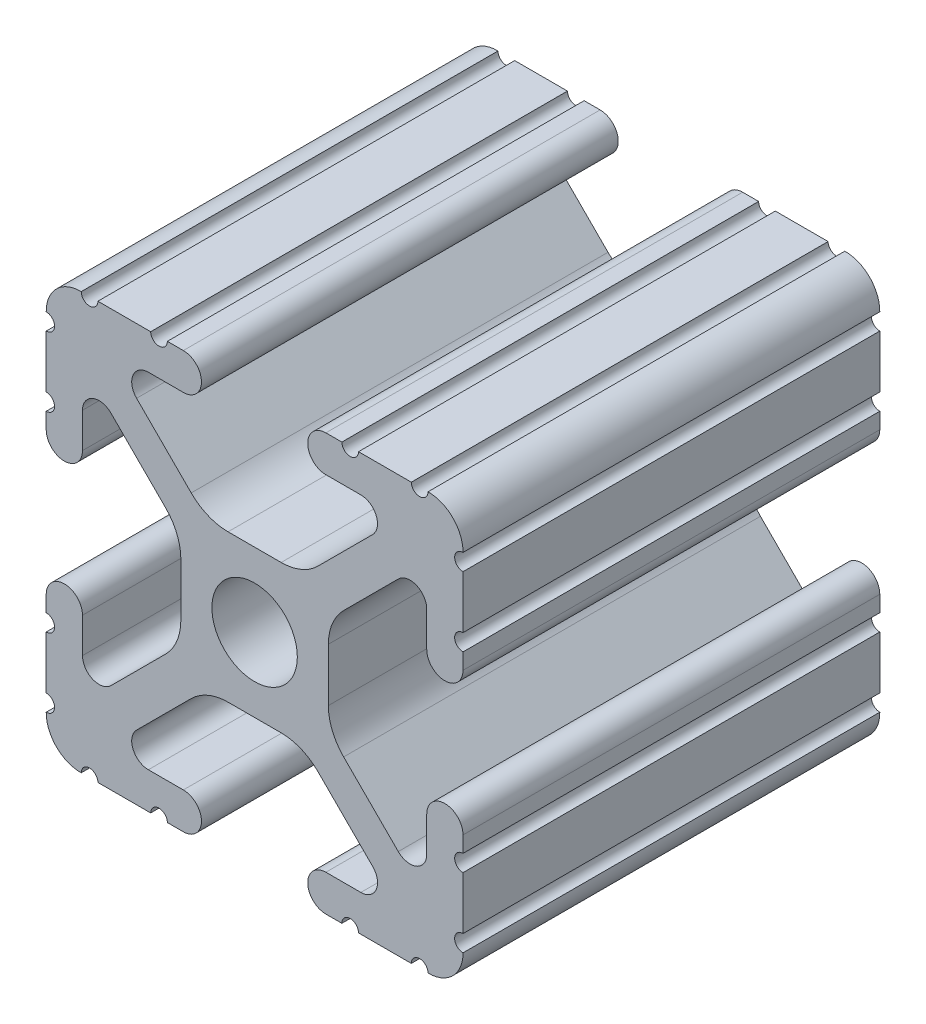
SolidWorks part; units mm, degrees
ref_plane "Front Plane" through (0, 0, 0) normal (0, 0, 1) x (1, 0, 0)
ref_plane "Top Plane" through (0, 0, 0) normal (0, 1, 0) x (1, 0, 0)
ref_plane "Right Plane" through (0, 0, 0) normal (1, 0, 0) x (0, 0, -1)
ref_plane "Plane1" through (0, 0, -25.4) normal (0, 0, -1) x (-1, 0, 0)
sketch "Sketch1" plane through (0, 0, -25.4) normal (0, 0, -1) x (-1, 0, 0)
  line L0 (12.7, -9.5504) -> (12.7, -6.3331)
  line L1 (12.7, -5.3171) -> (12.7, -4.3434)
  line L2 (10.4902, -4.3434) -> (10.4902, -6.4748)
  line L3 (8.7558, -7.1932) -> (5.4257, -3.8632)
  line L4 (4.4958, -1.6181) -> (4.4958, 1.6181)
  line L5 (5.4257, 3.8632) -> (8.7558, 7.1932)
  line L6 (10.4902, 6.4748) -> (10.4902, 4.3434)
  line L7 (12.7, 4.3434) -> (12.7, 5.3171)
  line L8 (12.7, 6.3331) -> (12.7, 9.5504)
  line L9 (9.5504, 12.7) -> (6.3331, 12.7)
  line L10 (5.3171, 12.7) -> (4.3434, 12.7)
  line L11 (4.3434, 10.4902) -> (6.4748, 10.4902)
  line L12 (7.1932, 8.7558) -> (3.8632, 5.4257)
  line L13 (1.6181, 4.4958) -> (-1.6181, 4.4958)
  line L14 (-3.8632, 5.4257) -> (-7.1932, 8.7558)
  line L15 (-6.4748, 10.4902) -> (-4.3434, 10.4902)
  line L16 (-4.3434, 12.7) -> (-5.3171, 12.7)
  line L17 (-6.3331, 12.7) -> (-9.5504, 12.7)
  line L18 (-12.7, 9.5504) -> (-12.7, 6.3331)
  line L19 (-12.7, 5.3171) -> (-12.7, 4.3434)
  line L20 (-10.4902, 4.3434) -> (-10.4902, 6.4748)
  line L21 (-8.7558, 7.1932) -> (-5.4257, 3.8632)
  line L22 (-4.4958, 1.6181) -> (-4.4958, -1.6181)
  line L23 (-5.4257, -3.8632) -> (-8.7558, -7.1932)
  line L24 (-10.4902, -6.4748) -> (-10.4902, -4.3434)
  line L25 (-12.7, -4.3434) -> (-12.7, -5.3171)
  line L26 (-12.7, -6.3331) -> (-12.7, -9.5504)
  line L27 (-9.5504, -12.7) -> (-6.3331, -12.7)
  line L28 (-5.3171, -12.7) -> (-4.3434, -12.7)
  line L29 (-4.3434, -10.4902) -> (-6.4748, -10.4902)
  line L30 (-7.1932, -8.7558) -> (-3.8632, -5.4257)
  line L31 (-1.6181, -4.4958) -> (1.6181, -4.4958)
  line L32 (3.8632, -5.4257) -> (7.1932, -8.7558)
  line L33 (6.4748, -10.4902) -> (4.3434, -10.4902)
  line L34 (4.3434, -12.7) -> (5.3171, -12.7)
  line L35 (6.3331, -12.7) -> (9.5504, -12.7)
  arc A0 (12.6998, -10.5664) -> (12.7, -9.5504) centre (12.7, -10.0584) cw
  arc A1 (12.7, -6.3331) -> (12.7, -5.3171) centre (12.7, -5.8251) cw
  arc A2 (12.7, -4.3434) -> (10.4902, -4.3434) centre (11.5951, -4.3434) ccw
  arc A3 (10.4902, -6.4748) -> (8.7558, -7.1932) centre (9.4742, -6.4748) cw
  arc A4 (5.4257, -3.8632) -> (4.4958, -1.6181) centre (7.6708, -1.6181) cw
  arc A5 (4.4958, 1.6181) -> (5.4257, 3.8632) centre (7.6708, 1.6181) cw
  arc A6 (8.7558, 7.1932) -> (10.4902, 6.4748) centre (9.4742, 6.4748) cw
  arc A7 (10.4902, 4.3434) -> (12.7, 4.3434) centre (11.5951, 4.3434) ccw
  arc A8 (12.7, 5.3171) -> (12.7, 6.3331) centre (12.7, 5.8251) cw
  arc A9 (12.7, 9.5504) -> (12.6998, 10.5664) centre (12.7, 10.0584) cw
  arc A10 (12.6998, 10.5664) -> (10.5664, 12.6998) centre (10.5918, 10.5918) ccw
  arc A11 (10.5664, 12.6998) -> (9.5504, 12.7) centre (10.0584, 12.7) cw
  arc A12 (6.3331, 12.7) -> (5.3171, 12.7) centre (5.8251, 12.7) cw
  arc A13 (4.3434, 12.7) -> (4.3434, 10.4902) centre (4.3434, 11.5951) ccw
  arc A14 (6.4748, 10.4902) -> (7.1932, 8.7558) centre (6.4748, 9.4742) cw
  arc A15 (3.8632, 5.4257) -> (1.6181, 4.4958) centre (1.6181, 7.6708) cw
  arc A16 (-1.6181, 4.4958) -> (-3.8632, 5.4257) centre (-1.6181, 7.6708) cw
  arc A17 (-7.1932, 8.7558) -> (-6.4748, 10.4902) centre (-6.4748, 9.4742) cw
  arc A18 (-4.3434, 10.4902) -> (-4.3434, 12.7) centre (-4.3434, 11.5951) ccw
  arc A19 (-5.3171, 12.7) -> (-6.3331, 12.7) centre (-5.8251, 12.7) cw
  arc A20 (-9.5504, 12.7) -> (-10.5664, 12.6998) centre (-10.0584, 12.7) cw
  arc A21 (-10.5664, 12.6998) -> (-12.6998, 10.5664) centre (-10.5918, 10.5918) ccw
  arc A22 (-12.6998, 10.5664) -> (-12.7, 9.5504) centre (-12.7, 10.0584) cw
  arc A23 (-12.7, 6.3331) -> (-12.7, 5.3171) centre (-12.7, 5.8251) cw
  arc A24 (-12.7, 4.3434) -> (-10.4902, 4.3434) centre (-11.5951, 4.3434) ccw
  arc A25 (-10.4902, 6.4748) -> (-8.7558, 7.1932) centre (-9.4742, 6.4748) cw
  arc A26 (-5.4257, 3.8632) -> (-4.4958, 1.6181) centre (-7.6708, 1.6181) cw
  arc A27 (-4.4958, -1.6181) -> (-5.4257, -3.8632) centre (-7.6708, -1.6181) cw
  arc A28 (-8.7558, -7.1932) -> (-10.4902, -6.4748) centre (-9.4742, -6.4748) cw
  arc A29 (-10.4902, -4.3434) -> (-12.7, -4.3434) centre (-11.5951, -4.3434) ccw
  arc A30 (-12.7, -5.3171) -> (-12.7, -6.3331) centre (-12.7, -5.8251) cw
  arc A31 (-12.7, -9.5504) -> (-12.6998, -10.5664) centre (-12.7, -10.0584) cw
  arc A32 (-12.6998, -10.5664) -> (-10.5664, -12.6998) centre (-10.5918, -10.5918) ccw
  arc A33 (-10.5664, -12.6998) -> (-9.5504, -12.7) centre (-10.0584, -12.7) cw
  arc A34 (-6.3331, -12.7) -> (-5.3171, -12.7) centre (-5.8251, -12.7) cw
  arc A35 (-4.3434, -12.7) -> (-4.3434, -10.4902) centre (-4.3434, -11.5951) ccw
  arc A36 (-6.4748, -10.4902) -> (-7.1932, -8.7558) centre (-6.4748, -9.4742) cw
  arc A37 (-3.8632, -5.4257) -> (-1.6181, -4.4958) centre (-1.6181, -7.6708) cw
  arc A38 (1.6181, -4.4958) -> (3.8632, -5.4257) centre (1.6181, -7.6708) cw
  arc A39 (7.1932, -8.7558) -> (6.4748, -10.4902) centre (6.4748, -9.4742) cw
  arc A40 (4.3434, -10.4902) -> (4.3434, -12.7) centre (4.3434, -11.5951) ccw
  arc A41 (5.3171, -12.7) -> (6.3331, -12.7) centre (5.8251, -12.7) cw
  arc A42 (9.5504, -12.7) -> (10.5664, -12.6998) centre (10.0584, -12.7) cw
  arc A43 (10.5664, -12.6998) -> (12.6998, -10.5664) centre (10.5918, -10.5918) ccw
  circle A44 centre (0, 0) radius 2.6035
extrude "Boss-Extrude1" add sketch "Sketch1" against normal blind 25.4
